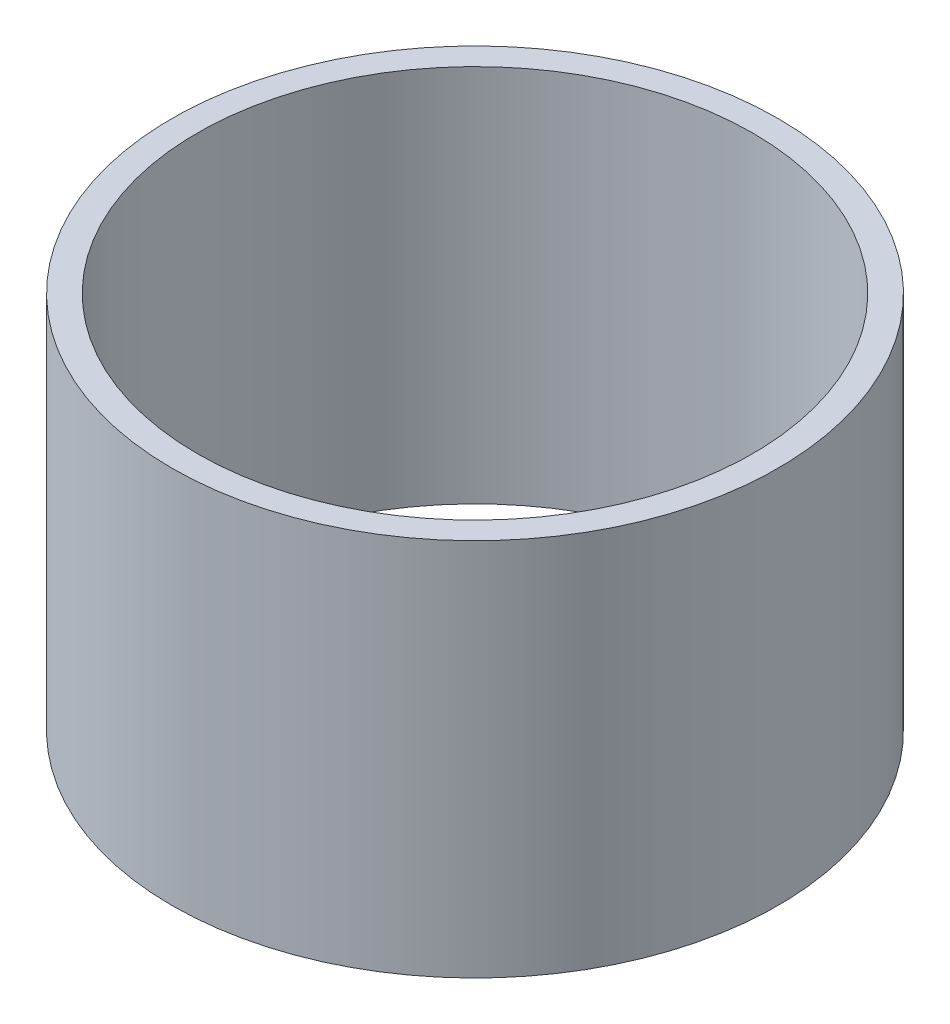
SolidWorks part; units mm, degrees
material "AISI 304"
ref_plane "前视基准面" through (0, 0, 0) normal (0, 0, 1) x (1, 0, 0)
ref_plane "上视基准面" through (0, 0, 0) normal (0, 1, 0) x (1, 0, 0)
ref_plane "右视基准面" through (0, 0, 0) normal (1, 0, 0) x (0, 0, -1)
other "Configuration Table"
sketch "草图1" plane through (0, 0, 0) normal (0, 1, 0) x (1, 0, 0)
  circle A0 centre (0, 0) radius 5.5
  circle A1 centre (0, 0) radius 6
  dimension "D1" = 11
  dimension "D2" = 12
extrude "凸台-拉伸1" add sketch "草图1" along normal blind 7.5
